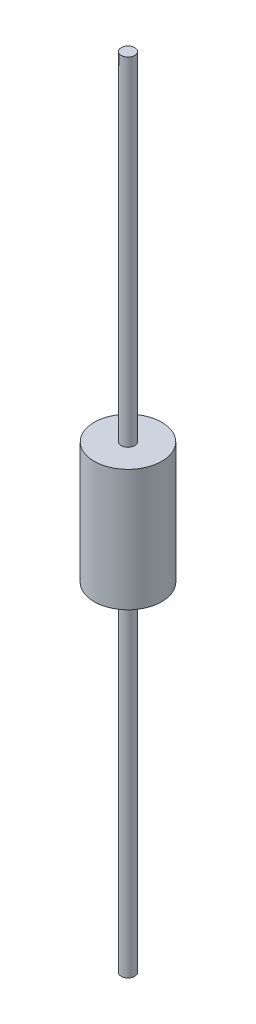
SolidWorks part; units mm, degrees
ref_plane "Front Plane" through (0, 0, 0) normal (0, 0, 1) x (1, 0, 0)
ref_plane "Top Plane" through (0, 0, 0) normal (0, 1, 0) x (1, 0, 0)
ref_plane "Right Plane" through (0, 0, 0) normal (1, 0, 0) x (0, 0, -1)
sketch "Sketch1" plane through (0, 0, 0) normal (0, 1, 0) x (1, 0, 0)
  circle A0 centre (0, 0) radius 2.5
  dimension "D1" = 5
extrude "Boss-Extrude1" add sketch "Sketch1" along normal mid plane 9
sketch "Sketch2" plane through (0, 4.5, 0) normal (0, 1, 0) x (1, 0, 0)
  circle A0 centre (0, 0) radius 0.5
  dimension "D1" = 1
extrude "Boss-Extrude2" add sketch "Sketch2" along normal blind 25
mirror "Mirror4" about plane through (0, 0, 0) normal (0, 1, 0) of "Boss-Extrude2"
